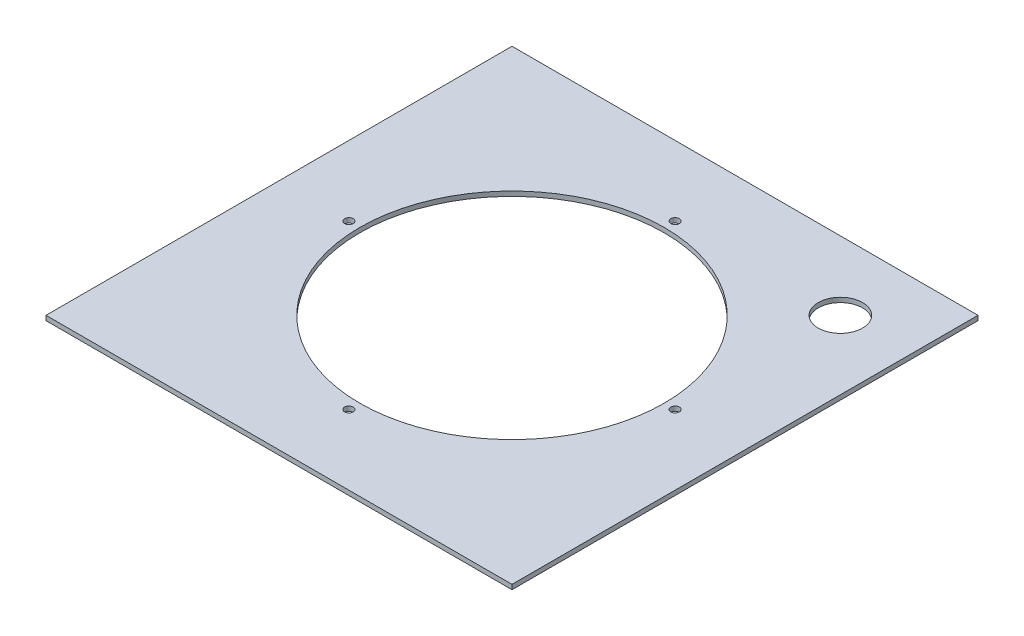
SolidWorks part; units mm, degrees
ref_plane "Front Plane" through (0, 0, 0) normal (0, 0, 1) x (1, 0, 0)
ref_plane "Top Plane" through (0, 0, 0) normal (0, 1, 0) x (1, 0, 0)
ref_plane "Right Plane" through (0, 0, 0) normal (1, 0, 0) x (0, 0, -1)
sketch "Sketch1" plane through (0, 0, 0) normal (0, 1, 0) x (1, 0, 0)
  line L1 (0, 0) -> (300, 0)
  line L2 (0, 0) -> (0, -300)
  line L3 (0, -300) -> (300, -300)
  line L4 (300, 0) -> (300, -300)
  dimension "D1" = 300
  dimension "D2" = 300
extrude "Boss-Extrude1" add sketch "Sketch1" along normal blind 3
sketch "Sketch2" plane through (0, 3, 0) normal (0, 1, 0) x (1, 0, 0)
  line L0 (300, -300) -> (300, 0) construction
  line L1 (0, -300) -> (300, -300) construction
  line L2 (150, -150) -> (300, 0) construction
  line L3 (300, 0) -> (300, -300) construction
  line L4 (0, 0) -> (300, 0) construction
  circle A0 centre (150, -150) radius 98
  circle A1 centre (255.7125, -44.2875) radius 14.255
  point P5 (300, -150)
  point P8 (150, -300)
  dimension "D1" = 196
  dimension "D3" = 28.51
  dimension "D2" = 149.5
  dimension "D4" = 44.2875
  dimension "D5" = 44.2875
extrude "Cut-Extrude1" cut sketch "Sketch2" against normal up to next
sketch "Sketch4" plane through (0, 3, 0) normal (0, 1, 0) x (1, 0, 0)
  line L0 (0, -300) -> (300, -300) construction
  line L1 (0, 0) -> (0, -300) construction
  line L2 (300, 0) -> (300, -300) construction
  line L3 (0, 0) -> (300, 0) construction
  circle A0 centre (150, -150) radius 105 construction
  circle A2 centre (45, -150) radius 2.75
  circle A3 centre (255, -150) radius 2.75
  circle A4 centre (150, -255) radius 2.75
  circle A5 centre (150, -45) radius 2.75
  dimension "D1" = 210
  dimension "D2" = 5.5
  dimension "D3" = 5.5
  dimension "D4" = 5.5
  dimension "D5" = 5.5
  dimension "D7" = 45
  dimension "D8" = 45
  dimension "D9" = 45
  dimension "D6" = 45
extrude "Cut-Extrude3" cut sketch "Sketch4" against normal through all contours A2 | A5 | A3 | A4
sketch "Sketch5" plane through (0, 3, 0) normal (0, 1, 0) x (1, 0, 0)
  line L0 (300, -300) -> (300, 0) construction
  line L1 (0, 0) -> (300, 0)
  line L2 (0, 0) -> (0, -270)
  line L3 (0, -270) -> (300, -270)
  line L4 (300, 0) -> (300, -270)
  line L5 (0, -300) -> (300, -300) construction
  dimension "D1" = 30
sketch "Sketch6" plane through (0, 3, 0) normal (0, 1, 0) x (1, 0, 0)
  line L0 (300, -300) -> (300, 0) construction
  line L1 (0, -300) -> (300, -300)
  line L2 (0, -300) -> (0, -270)
  line L3 (0, -270) -> (300, -270)
  line L4 (300, -300) -> (300, -270)
  dimension "D1" = 30
